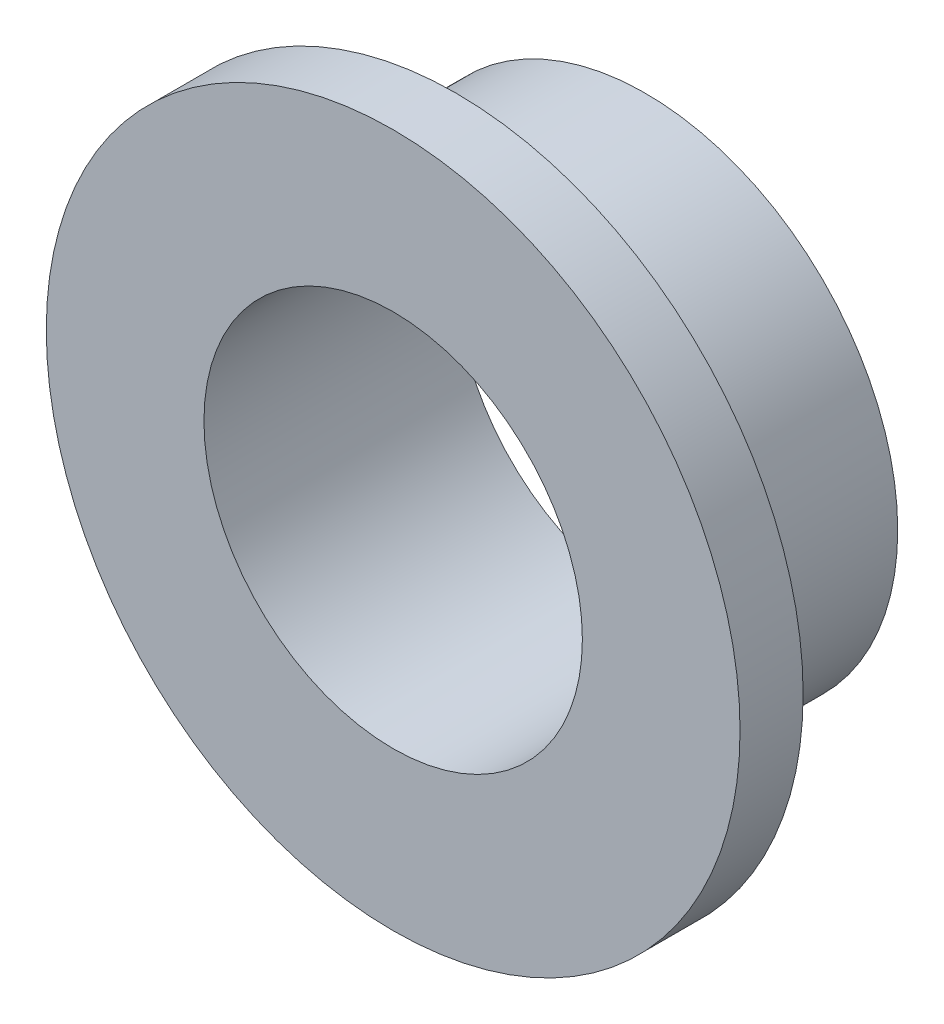
SolidWorks part; units mm, degrees
material "Tin Bearing Bronze"
ref_plane "Front Plane" through (0, 0, 0) normal (0, 0, 1) x (1, 0, 0)
ref_plane "Top Plane" through (0, 0, 0) normal (0, 1, 0) x (1, 0, 0)
ref_plane "Right Plane" through (0, 0, 0) normal (1, 0, 0) x (0, 0, -1)
sketch "Sketch1" plane through (0, 0, 0) normal (0, 0, 1) x (1, 0, 0)
  circle A0 centre (0, 0) radius 4.7625
  circle A1 centre (0, 0) radius 6.35
  dimension "D1" = 9.525
  dimension "D2" = 12.7
extrude "Boss-Extrude1" add sketch "Sketch1" along normal blind 6.35
sketch "Sketch2" plane through (0, 0, 6.35) normal (0, 0, 1) x (1, 0, 0)
  circle A0 centre (0, 0) radius 4.7625
  circle A1 centre (0, 0) radius 8.7312
  dimension "D1" = 9.525
  dimension "D2" = 17.4625
extrude "Boss-Extrude2" add sketch "Sketch2" against normal blind 1.5875
